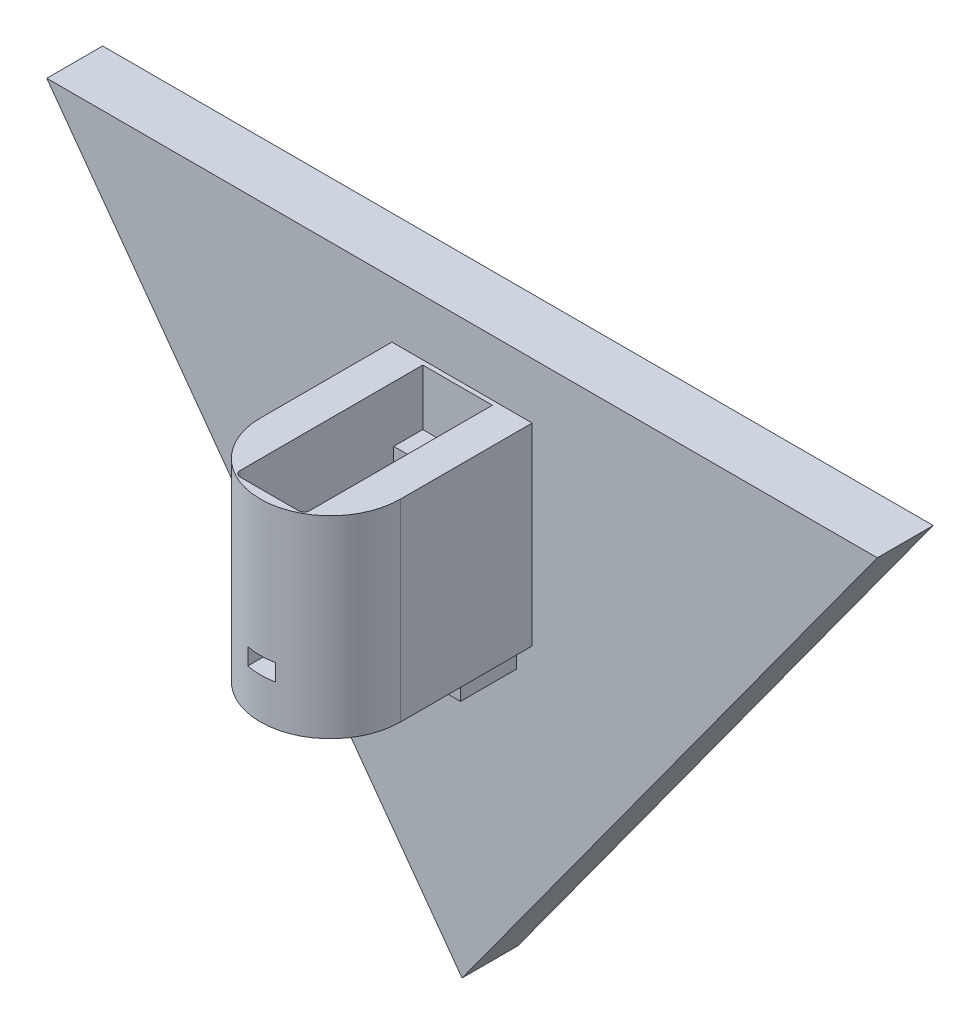
SolidWorks part; units mm, degrees
ref_plane "Front Plane" through (0, 0, 0) normal (0, 0, 1) x (1, 0, 0)
ref_plane "Top Plane" through (0, 0, 0) normal (0, 1, 0) x (1, 0, 0)
ref_plane "Right Plane" through (0, 0, 0) normal (1, 0, 0) x (0, 0, -1)
sketch "Sketch4" plane through (0, 0, 0) normal (0, 0, 1) x (1, 0, 0)
  line L0 (55, 0) -> (-55, 0) construction
  line L1 (-6.23, -9.975) -> (6.23, -9.975)
  line L2 (-6.23, -9.975) -> (-6.23, 7.275)
  line L3 (-6.23, 7.275) -> (6.23, 7.275)
  line L4 (6.23, -9.975) -> (6.23, 7.275)
  point P4 (0, 7.275)
  dimension "D1" = 12.46
  dimension "D2" = 17.25
  dimension "D3" = 9.975
extrude "Boss-Extrude3" add sketch "Sketch4" along normal blind 6
sketch "Sketch8" plane through (0, -9.975, 0) normal (0, -1, 0) x (-1, 0, 0)
  circle A0 centre (0, -23.55) radius 12.5468
  circle A1 centre (0, -23.55) radius 11.15
  dimension "D1" = 22.3
  dimension "D2" = 23.55
extrude "Boss-Extrude6" add sketch "Sketch8" along normal blind 7.3 and the other way up to surface (17.25 mm away) other way up to face at (0, 7.275, 3)
sketch "Sketch5" plane through (0, 7.275, 0) normal (0, 1, 0) x (1, 0, 0)
  line L8 (12.5468, -23.55) -> (12.5468, 0)
  line L9 (12.5468, 0) -> (6.23, 0)
  line L10 (-12.5468, -23.55) -> (-12.5468, 0)
  line L11 (-12.5468, 0) -> (-6.23, 0)
  line L12 (-6.23, 0) -> (-6.23, -29.7)
  line L14 (6.23, -29.7) -> (6.23, 0)
  line L15 (-6.23, -29.7) -> (6.23, -29.7)
  line L16 (6.23, -6) -> (-6.23, -6) construction
  circle A0 centre (0, -23.55) radius 12.5468 construction
  arc A1 (-12.5468, -23.55) -> (12.5468, -23.55) centre (0, -23.55) ccw
  dimension "D1" = 23.7
  dimension "D2" = 23.55
extrude "Boss-Extrude4" add sketch "Sketch5" against normal up to surface (17.25 mm away) up to face at (0, -9.975, 3)
sketch "Sketch6" plane through (0, 7.275, 0) normal (0, 1, 0) x (1, 0, 0)
  line L0 (6.23, -6) -> (-6.23, -6) construction
  line L3 (6.23, -29.7) -> (-6.23, -29.7) construction
  circle A0 centre (0, -3.6) radius 0.5
  circle A1 centre (0, -32.1) radius 0.5
  dimension "D1" = 1
  dimension "D3" = 1
  dimension "D2" = 2.4
  dimension "D4" = 2.4
extrude "Cut-Extrude1" cut sketch "Sketch6" against normal blind 20
chamfer "Chamfer1" distance 0.5 angle 60 2 edges at (0, 7.275, 4.1) (0, 7.275, 32.6)
sketch "Sketch10" plane through (0, 7.275, 0) normal (0, 1, 0) x (1, 0, 0)
  line L1 (-6.23, -6) -> (6.23, -6)
  line L2 (-6.23, -6) -> (-6.23, -29.7)
  line L3 (-6.23, -29.7) -> (6.23, -29.7)
  line L4 (6.23, -6) -> (6.23, -29.7)
extrude "Cut-Extrude3" cut sketch "Sketch10" against normal up to surface (17.25 mm away) up to face at (-0.5, -9.975, 32.1)
ref_plane "Plane1" through (0, 0, 36.0968) normal (0, 0, 1) x (1, 0, 0)
sketch "Sketch11" plane through (0, 0, 36.0968) normal (0, 0, 1) x (1, 0, 0)
  line L0 (-11.15, -9.975) -> (11.15, -9.975) construction
  line L1 (-2.5, -6.975) -> (2.5, -6.975)
  line L2 (-2.5, -6.975) -> (-2.5, -9.975)
  line L3 (-2.5, -9.975) -> (2.5, -9.975)
  line L4 (2.5, -6.975) -> (2.5, -9.975)
  point P4 (0, -6.975)
  dimension "D1" = 0
  dimension "D2" = 5
  dimension "D3" = 3
extrude "Cut-Extrude4" cut sketch "Sketch11" against normal up to next
sketch "Sketch13" plane through (0, -17.275, 0) normal (0, -1, 0) x (1, 0, 0)
  line L0 (-12.5468, 23.55) -> (-12.5468, 0)
  line L1 (-12.5468, 0) -> (12.5468, 0)
  line L2 (12.5468, 0) -> (12.5468, 23.55)
  arc A0 (-12.5468, 23.55) -> (12.5468, 23.55) centre (0, 23.55) ccw
  point P3 (0, 0)
extrude "Boss-Extrude7" add sketch "Sketch13" against normal up to surface (7.3 mm away) up to face at (6.0145, -9.975, 27.3356)
sketch "Sketch15" plane through (0, 7.275, 0) normal (0, 1, 0) x (1, 0, 0)
  line L0 (-12.5468, 0) -> (12.5468, 0)
  line L1 (12.5468, 0) -> (12.5468, -23.55)
  line L2 (-12.5468, 0) -> (-12.5468, -23.55)
  line L3 (6.23, -6) -> (6.23, -29.7) construction
  line L4 (-6.23, -0.8) -> (6.23, -0.8)
  line L5 (-6.23, -0.8) -> (-6.23, -33.5)
  line L6 (-5.23, -34.5) -> (5.23, -34.5)
  line L7 (6.23, -0.8) -> (6.23, -33.5)
  arc A0 (-12.5468, -23.55) -> (12.5468, -23.55) centre (0, -23.55) ccw
  circle A1 centre (0, -3.6) radius 0.5 construction
  arc A2 (5.23, -34.5) -> (6.23, -33.5) centre (5.23, -33.5) ccw
  arc A3 (-6.23, -33.5) -> (-5.23, -34.5) centre (-5.23, -33.5) ccw
  point P15 (0, -0.8)
  dimension "D1" = 0.8
  dimension "D3" = 1
  dimension "D2" = 2.8
  dimension "D4" = 0
  dimension "D5" = 34.5
extrude "Boss-Extrude9" add sketch "Sketch15" along normal blind 10
sketch "Sketch16" plane through (0, -17.275, 0) normal (0, -1, 0) x (1, 0, 0)
  circle A0 centre (0, 23.55) radius 11.15
  circle A1 centre (0, 23.55) radius 7.15
  circle A2 centre (0, 23.55) radius 11.15 construction
  dimension "D1" = 14.3
extrude "Boss-Extrude10" add sketch "Sketch16" against normal up to surface (7.3 mm away) up to face at (6.0145, -9.975, 27.3356)
sketch "Sketch17" plane through (0, -17.275, 0) normal (0, -1, 0) x (1, 0, 0)
  circle A0 centre (0, 23.55) radius 10.15
  circle A1 centre (0, 23.55) radius 7.15
  circle A2 centre (0, 23.55) radius 7.15 construction
  dimension "D1" = 20.3
extrude "Cut-Extrude5" cut sketch "Sketch17" against normal blind 1.3
sketch "Sketch18" plane through (0, -17.275, 0) normal (0, -1, 0) x (1, 0, 0)
  line L0 (-12.5468, 0) -> (12.5468, 0) construction
  line L1 (6.73, 0) -> (9.73, 0)
  line L2 (6.73, 0) -> (6.73, 10)
  line L3 (6.73, 10) -> (9.73, 10)
  line L4 (9.73, 0) -> (9.73, 10)
  line L6 (2.214, 0) -> (5.214, 0)
  line L7 (2.214, 0) -> (2.214, 10)
  line L8 (2.214, 10) -> (5.214, 10)
  line L9 (5.214, 0) -> (5.214, 10)
  line L12 (6.23, 27.0585) -> (6.23, 20.0415) construction
  point P10 (12.5468, 5.802)
  point P11 (0, 0)
  point P13 (0, 0)
  point P17 (-37.0973, 23.6701)
  dimension "D1" = 3
  dimension "D2" = 1.516
  dimension "D3" = 3
  dimension "D4" = 10
  dimension "D5" = 0.5
extrude "Boss-Extrude11" add sketch "Sketch18" along normal blind 5
sketch "Sketch1" plane through (0, 0, 0) normal (0, 0, 1) x (1, 0, 0)
  line L0 (0, -75) -> (74.3071, 27.275)
  line L1 (74.3071, 27.275) -> (-74.3071, 27.275)
  line L2 (-74.3071, 27.275) -> (0, -75)
  line L3 (6.23, 17.275) -> (-6.23, 17.275) construction
  line L4 (13.8015, 0) -> (-13.8015, 0) construction
  point P10 (0, 27.275)
  dimension "D2" = 10
  dimension "D1" = 72
  dimension "D3" = 75
extrude "Offset R" add sketch "Sketch1" against normal blind 10 contours L2 L0 L1
